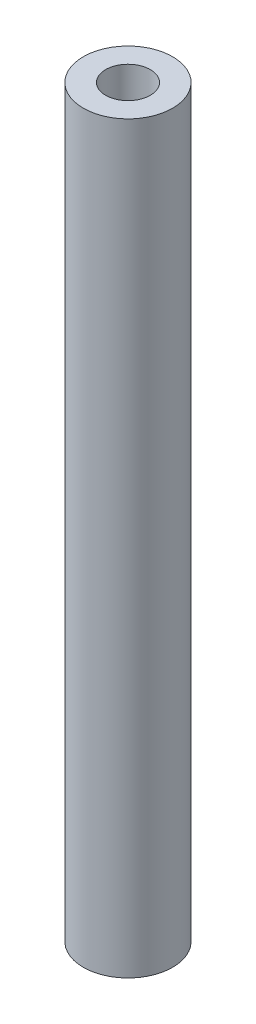
SolidWorks part; units mm, degrees
ref_plane "Front Plane" through (0, 0, 0) normal (0, 0, 1) x (1, 0, 0)
ref_plane "Top Plane" through (0, 0, 0) normal (0, 1, 0) x (1, 0, 0)
ref_plane "Right Plane" through (0, 0, 0) normal (1, 0, 0) x (0, 0, -1)
sketch "Sketch1" plane through (0, 0, 0) normal (0, 1, 0) x (1, 0, 0)
  circle A0 centre (0, 0) radius 6
  circle A1 centre (0, 0) radius 1.5
  dimension "D1" = 3
  dimension "D2" = 12
extrude "Boss-Extrude1" add sketch "Sketch1" along normal blind 100
sketch "Sketch2" plane through (0, 100, 0) normal (0, 1, 0) x (1, 0, 0)
  circle A0 centre (0, 0) radius 3
  dimension "D1" = 6
extrude "Cut-Extrude1" cut sketch "Sketch2" against normal blind 5
sketch "Sketch3" plane through (0, 0, 0) normal (0, -1, 0) x (1, 0, 0)
  circle A0 centre (0, 0) radius 3
  dimension "D1" = 6
extrude "Cut-Extrude2" cut sketch "Sketch3" against normal blind 5
